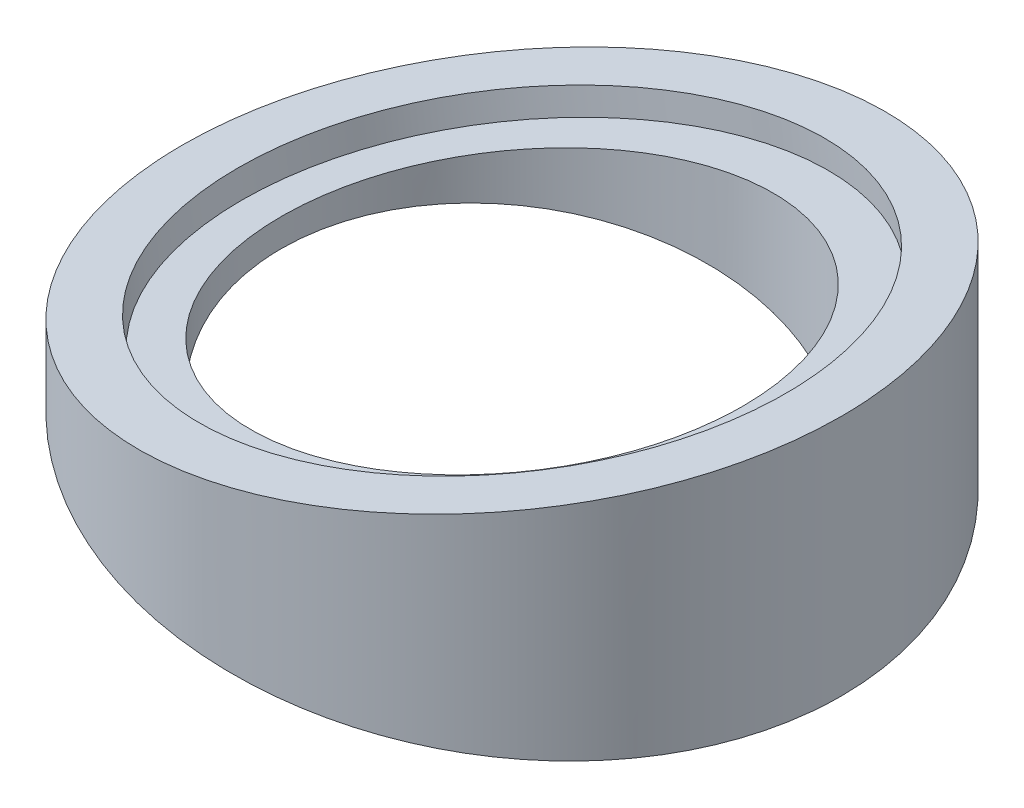
SolidWorks part; units mm, degrees
ref_plane "前视基准面" through (0, 0, 0) normal (0, 0, 1) x (1, 0, 0)
ref_plane "上视基准面" through (0, 0, 0) normal (0, 1, 0) x (1, 0, 0)
ref_plane "右视基准面" through (0, 0, 0) normal (1, 0, 0) x (0, 0, -1)
sketch "草图1" plane through (0, 0, 0) normal (0, 1, 0) x (1, 0, 0)
  circle A0 centre (0, 0) radius 25
  dimension "D1" = 50
extrude "凸台-拉伸1" add sketch "草图1" along normal blind 40
sketch "草图2" plane through (0, 40, 0) normal (0, 1, 0) x (1, 0, 0)
  circle A0 centre (0, 0) radius 17.5
  dimension "D1" = 35
extrude "切除-拉伸1" cut sketch "草图2" against normal blind 72
sketch "草图3" plane through (0, 0, 0) normal (0, 0, 1) x (1, 0, 0)
  line L6 (-25, 22) -> (25, 29.1889)
  line L7 (-25, 40) -> (-25, 0) construction
  line L8 (25, 0) -> (25, 40) construction
  line L9 (25, 29.1889) -> (25, 44.2243)
  line L10 (25, 44.2243) -> (-25, 43.7529)
  line L11 (-25, 43.7529) -> (-25, 22)
  line L13 (-25, 20) -> (25, 20) construction
  line L14 (25, -4.2243) -> (-25, -3.7529)
  line L15 (25, 10.8111) -> (25, -4.2243)
  line L16 (-25, 18) -> (25, 10.8111)
  line L17 (-25, -3.7529) -> (-25, 18)
  dimension "D1" = 2
  dimension "D2" = 8.182
extrude "切除-拉伸2" cut sketch "草图3" against normal mid plane 77
sketch "草图6" plane through (-3.6054, 25.0761, 0) normal (-0.1423, 0.9898, 0) x (0.9898, 0.1423, 0)
  circle A0 centre (3.6425, 0) radius 21
  ellipse E0 centre (3.6425, 0) end of major axis (21.3224, 0) minor radius 17.5 construction
  point P2 (7.2297, 0)
  point P3 (3.4647, 0)
  dimension "D1" = 42
extrude "切除-拉伸6" cut sketch "草图6" against normal blind 2
sketch "草图7" plane through (2.0293, 14.1138, 0) normal (-0.1423, -0.9898, 0) x (0.9898, -0.1423, 0)
  circle A0 centre (-2.0501, 0) radius 21
  ellipse E0 centre (-2.0501, 0) end of major axis (-19.7301, 0) minor radius 17.5 construction
  dimension "D1" = 42
extrude "切除-拉伸7" cut sketch "草图7" against normal blind 2
